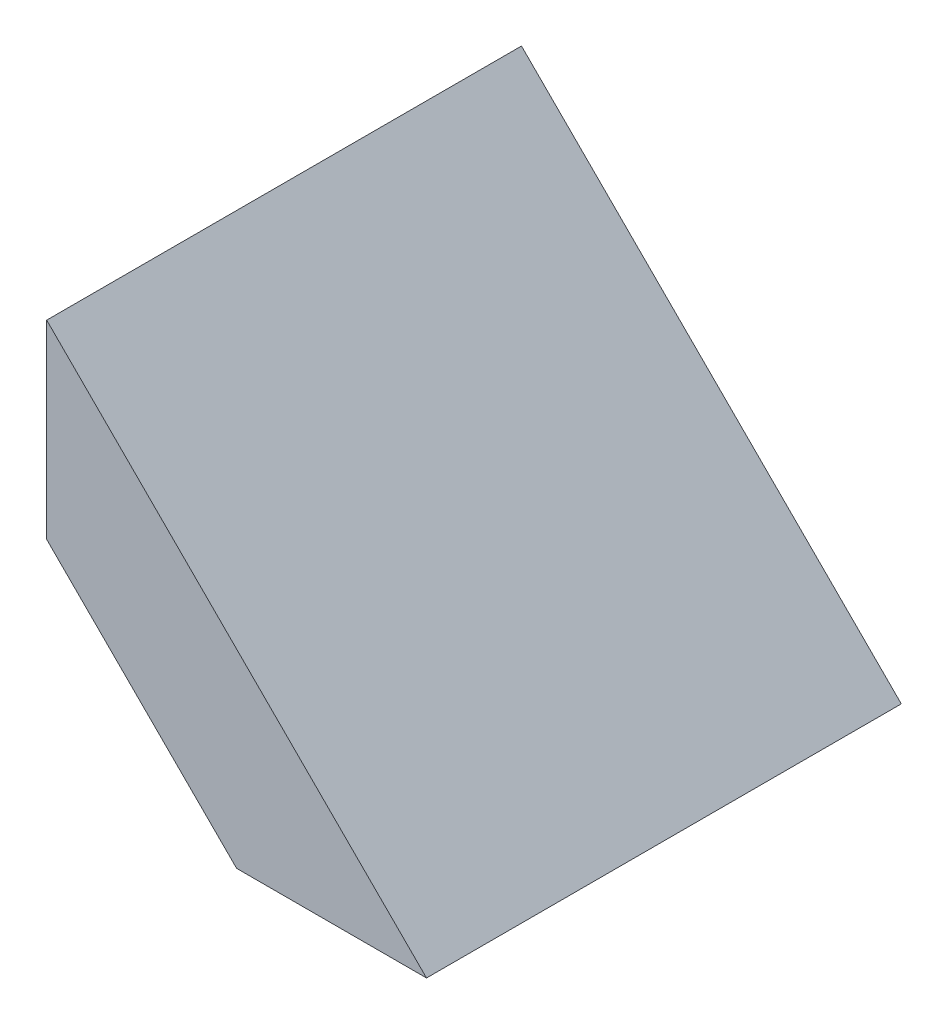
SolidWorks part; units mm, degrees
ref_plane "Front Plane" through (0, 0, 0) normal (0, 0, 1) x (1, 0, 0)
ref_plane "Top Plane" through (0, 0, 0) normal (0, 1, 0) x (1, 0, 0)
ref_plane "Right Plane" through (0, 0, 0) normal (1, 0, 0) x (0, 0, -1)
sketch "Sketch1" plane through (0, 0, 0) normal (0, 0, 1) x (1, 0, 0)
  line L0 (-20, 10) -> (-20, 20)
  line L1 (-20, 20) -> (0, 0)
  line L2 (0, 0) -> (-10, 0)
  line L3 (-10, 0) -> (-20, 10)
  dimension "D1" = 10
  dimension "D2" = 10
  dimension "D3" = 10
  dimension "D4" = 10
extrude "Boss-Extrude1" add sketch "Sketch1" along normal blind 25
